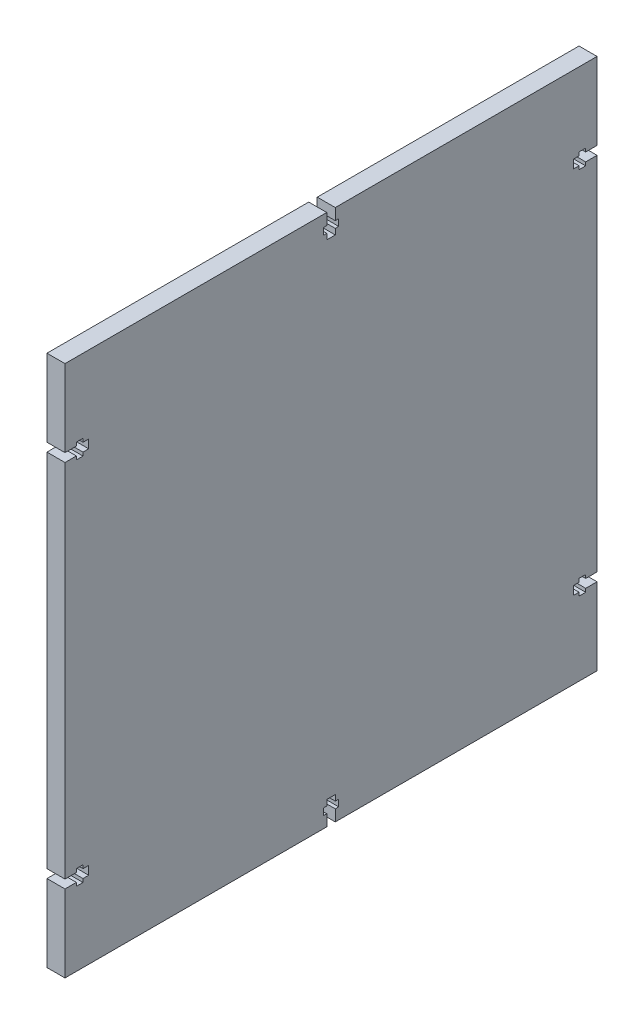
SolidWorks part; units mm, degrees
ref_plane "Front" through (0, 0, 0) normal (0, 0, 1) x (1, 0, 0)
ref_plane "Top" through (0, 0, 0) normal (0, 1, 0) x (1, 0, 0)
ref_plane "Right" through (0, 0, 0) normal (1, 0, 0) x (0, 0, -1)
sketch "Sketch1" plane through (0, 0, 0) normal (1, 0, 0) x (0, 0, -1)
  line L1 (-93.65, -93.65) -> (93.65, -93.65)
  line L2 (-93.65, -93.65) -> (-93.65, 93.65)
  line L3 (-93.65, 93.65) -> (93.65, 93.65)
  line L4 (93.65, -93.65) -> (93.65, 93.65)
  line L5 (-93.65, -93.65) -> (93.65, 93.65) construction
  line L6 (-93.65, 93.65) -> (93.65, -93.65) construction
  point P0 (0, 0)
  dimension "D1" = 187.3
  dimension "D2" = 187.3
extrude "Boss-Extrude1" add sketch "Sketch1" along normal blind 6.35
sketch "Sketch3" plane through (6.35, 0, 0) normal (1, 0, 0) x (0, 0, -1)
  line L0 (-93.65, 66.5) -> (-89.65, 66.5)
  line L1 (-93.65, 66.5) -> (-93.65, 63.5)
  line L2 (-93.65, 63.5) -> (-89.65, 63.5)
  line L3 (-89.65, 63.5) -> (-89.65, 62.29)
  line L4 (-89.65, 67.71) -> (-87.3, 67.71)
  line L5 (-89.65, 67.71) -> (-89.65, 66.5)
  line L6 (-89.65, 62.29) -> (-87.3, 62.29)
  line L7 (-87.3, 67.71) -> (-87.3, 66.5)
  line L8 (-87.3, 66.5) -> (-85.3, 66.5)
  line L9 (-87.3, 63.5) -> (-85.3, 63.5)
  line L10 (-85.3, 66.5) -> (-85.3, 63.5)
  line L11 (-87.3, 63.5) -> (-87.3, 62.29)
  line L12 (-93.65, 0) -> (93.65, 0) construction
  line L13 (-87.3, -63.5) -> (-87.3, -62.29)
  line L14 (-85.3, -66.5) -> (-85.3, -63.5)
  line L15 (-87.3, -63.5) -> (-85.3, -63.5)
  line L16 (-87.3, -66.5) -> (-85.3, -66.5)
  line L17 (-87.3, -67.71) -> (-87.3, -66.5)
  line L18 (-89.65, -62.29) -> (-87.3, -62.29)
  line L19 (-89.65, -67.71) -> (-89.65, -66.5)
  line L20 (-89.65, -67.71) -> (-87.3, -67.71)
  line L21 (-89.65, -63.5) -> (-89.65, -62.29)
  line L22 (-93.65, -63.5) -> (-89.65, -63.5)
  line L23 (-93.65, -66.5) -> (-93.65, -63.5)
  line L24 (-93.65, -66.5) -> (-89.65, -66.5)
  line L25 (0, 93.65) -> (0, -93.65) construction
  line L26 (93.65, -66.5) -> (89.65, -66.5)
  line L27 (93.65, -66.5) -> (93.65, -63.5)
  line L28 (93.65, -63.5) -> (89.65, -63.5)
  line L29 (89.65, -63.5) -> (89.65, -62.29)
  line L30 (89.65, -67.71) -> (87.3, -67.71)
  line L31 (89.65, -67.71) -> (89.65, -66.5)
  line L32 (89.65, -62.29) -> (87.3, -62.29)
  line L33 (87.3, -67.71) -> (87.3, -66.5)
  line L34 (87.3, -66.5) -> (85.3, -66.5)
  line L35 (87.3, -63.5) -> (85.3, -63.5)
  line L36 (85.3, -66.5) -> (85.3, -63.5)
  line L37 (87.3, -63.5) -> (87.3, -62.29)
  line L38 (87.3, 63.5) -> (87.3, 62.29)
  line L39 (85.3, 66.5) -> (85.3, 63.5)
  line L40 (87.3, 63.5) -> (85.3, 63.5)
  line L41 (87.3, 66.5) -> (85.3, 66.5)
  line L42 (87.3, 67.71) -> (87.3, 66.5)
  line L43 (89.65, 62.29) -> (87.3, 62.29)
  line L44 (89.65, 67.71) -> (89.65, 66.5)
  line L45 (89.65, 67.71) -> (87.3, 67.71)
  line L46 (89.65, 63.5) -> (89.65, 62.29)
  line L47 (93.65, 63.5) -> (89.65, 63.5)
  line L48 (93.65, 66.5) -> (93.65, 63.5)
  line L49 (93.65, 66.5) -> (89.65, 66.5)
  line L50 (-1.5, 93.65) -> (-1.5, 89.65)
  line L51 (2.71, 89.65) -> (2.71, 87.3)
  line L52 (1.5, 93.65) -> (1.5, 89.65)
  line L53 (1.5, 87.3) -> (2.71, 87.3)
  line L54 (-2.71, 89.65) -> (-1.5, 89.65)
  line L55 (-1.5, 87.3) -> (-1.5, 85.3)
  line L56 (-1.5, 93.65) -> (1.5, 93.65)
  line L57 (-2.71, 89.65) -> (-2.71, 87.3)
  line L58 (1.5, 87.3) -> (1.5, 85.3)
  line L59 (1.5, 89.65) -> (2.71, 89.65)
  line L60 (-1.5, 85.3) -> (1.5, 85.3)
  line L61 (-2.71, 87.3) -> (-1.5, 87.3)
  line L62 (-2.71, -87.3) -> (-1.5, -87.3)
  line L63 (-1.5, -85.3) -> (1.5, -85.3)
  line L64 (1.5, -89.65) -> (2.71, -89.65)
  line L65 (1.5, -87.3) -> (1.5, -85.3)
  line L66 (-2.71, -89.65) -> (-2.71, -87.3)
  line L67 (-1.5, -93.65) -> (1.5, -93.65)
  line L68 (-1.5, -87.3) -> (-1.5, -85.3)
  line L69 (-2.71, -89.65) -> (-1.5, -89.65)
  line L70 (1.5, -87.3) -> (2.71, -87.3)
  line L71 (1.5, -93.65) -> (1.5, -89.65)
  line L72 (2.71, -89.65) -> (2.71, -87.3)
  line L73 (-1.5, -93.65) -> (-1.5, -89.65)
extrude "Cut-Extrude2" cut sketch "Sketch3" against normal through all
